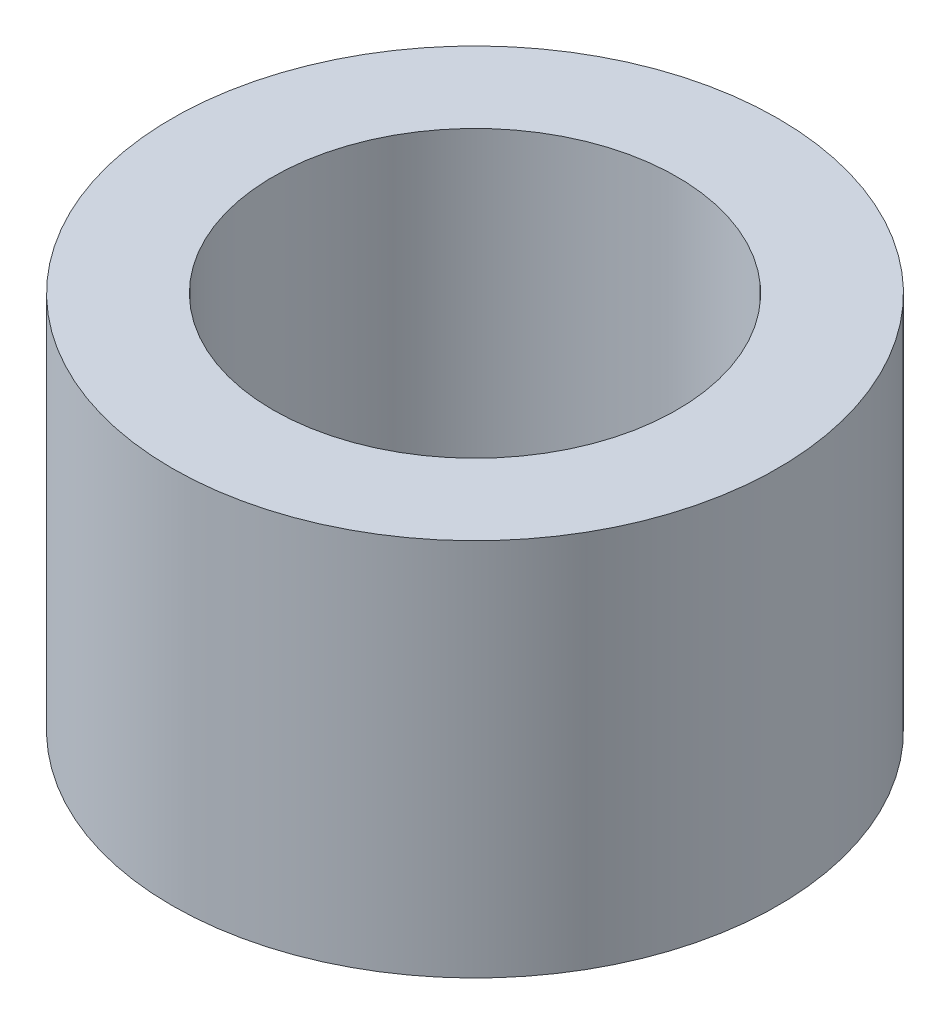
SolidWorks part; units mm, degrees
ref_plane "Front Plane" through (0, 0, 0) normal (0, 0, 1) x (1, 0, 0)
ref_plane "Top Plane" through (0, 0, 0) normal (0, 1, 0) x (1, 0, 0)
ref_plane "Right Plane" through (0, 0, 0) normal (1, 0, 0) x (0, 0, -1)
sketch "Sketch1" plane through (0, 0, 0) normal (0, 1, 0) x (1, 0, 0)
  circle A0 centre (0, 0) radius 4
  circle A1 centre (0, 0) radius 6
extrude "Boss-Extrude1" add sketch "Sketch1" along normal blind 7.5
